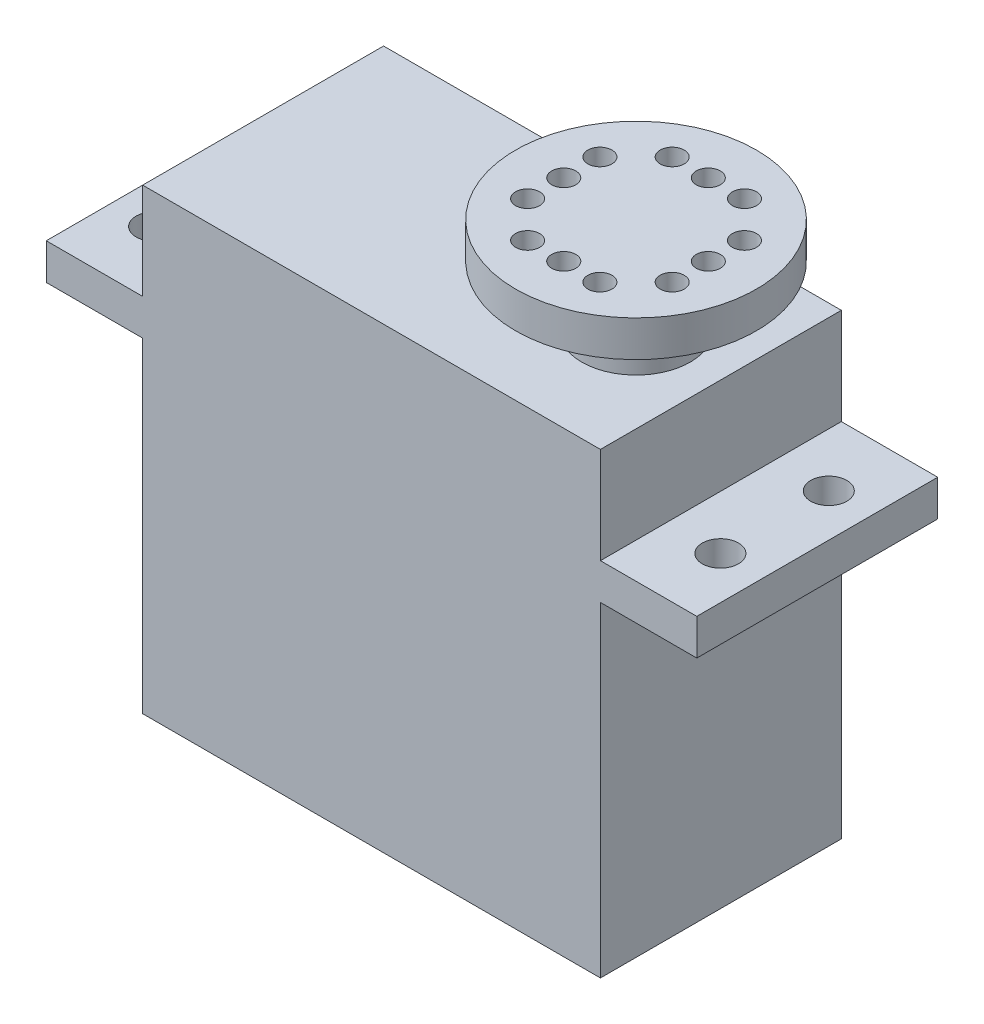
SolidWorks part; units mm, degrees
ref_plane "Front Plane" through (0, 0, 0) normal (0, 0, 1) x (1, 0, 0)
ref_plane "Top Plane" through (0, 0, 0) normal (0, 1, 0) x (1, 0, 0)
ref_plane "Right Plane" through (0, 0, 0) normal (1, 0, 0) x (0, 0, -1)
sketch "Sketch1" plane through (0, 0, 0) normal (0, 0, 1) x (1, 0, 0)
  line L1 (0, 0) -> (38, 0)
  line L2 (0, 0) -> (0, 38)
  line L3 (0, 38) -> (38, 38)
  line L4 (38, 0) -> (38, 38)
  line L9 (-8, 30) -> (46, 30)
  line L10 (-8, 30) -> (-8, 27)
  line L11 (-8, 27) -> (46, 27)
  line L12 (46, 30) -> (46, 27)
  dimension "D1" = 38
  dimension "D2" = 38
  dimension "D3" = 8
  dimension "D4" = 8
  dimension "D5" = 8
  dimension "D6" = 3
extrude "Boss-Extrude1" add sketch "Sketch1" along normal blind 20 contours L11 L2 L1 L4 | L2 L11 L4 L9 | L2 L9 L4 L3 | L12 L9 L4 L11 | L10 L11 L2 L9
sketch "Sketch2" plane through (0, 38, 0) normal (0, 1, 0) x (1, 0, 0)
  line L0 (0, -10) -> (38, -10) construction
  line L1 (0, -20) -> (0, 0) construction
  line L2 (38, -20) -> (38, 0) construction
  circle A0 centre (30.9563, -10) radius 4.5
  dimension "D1" = 9
extrude "Boss-Extrude2" add sketch "Sketch2" along normal blind 5
sketch "Sketch3" plane through (0, 43, 0) normal (0, 1, 0) x (1, 0, 0)
  circle A0 centre (30.9563, -10) radius 10
  dimension "D1" = 20
extrude "Boss-Extrude3" add sketch "Sketch3" along normal blind 3
sketch "Sketch4" plane through (0, 30, 0) normal (0, 1, 0) x (1, 0, 0)
  circle A0 centre (42.4563, -14.5) radius 1.5
  circle A1 centre (42.4563, -5.5) radius 1.5
  circle A2 centre (-4.5437, -14.5) radius 1.5
  circle A3 centre (-4.5437, -5.5) radius 1.5
  dimension "D1" = 3
  dimension "D2" = 3
  dimension "D3" = 3
  dimension "D4" = 3
extrude "Cut-Extrude1" cut sketch "Sketch4" against normal blind 10
sketch "Sketch5" plane through (0, 46, 0) normal (0, 1, 0) x (1, 0, 0)
  line L0 (30.9563, 0) -> (30.9563, -20) construction
  line L1 (0, 0) -> (38, 0) construction
  circle A0 centre (30.9563, -10) radius 10 construction
  circle A1 centre (30.9563, -4) radius 1
  circle A2 centre (27.9563, -4) radius 1
  circle A3 centre (33.9563, -4) radius 1
  point P13 (30.9563, -10)
  dimension "D1" = 2
  dimension "D2" = 2
  dimension "D3" = 2
  dimension "D4" = 3
  dimension "D5" = 3
  dimension "D6" = 6
extrude "Cut-Extrude2" cut sketch "Sketch5" against normal up to next (3 mm away)
pattern_circular "CirPattern1" count 4 over 360 about axis through (30.9563, 0, 10) along (0, 1, 0) of "Cut-Extrude2"
